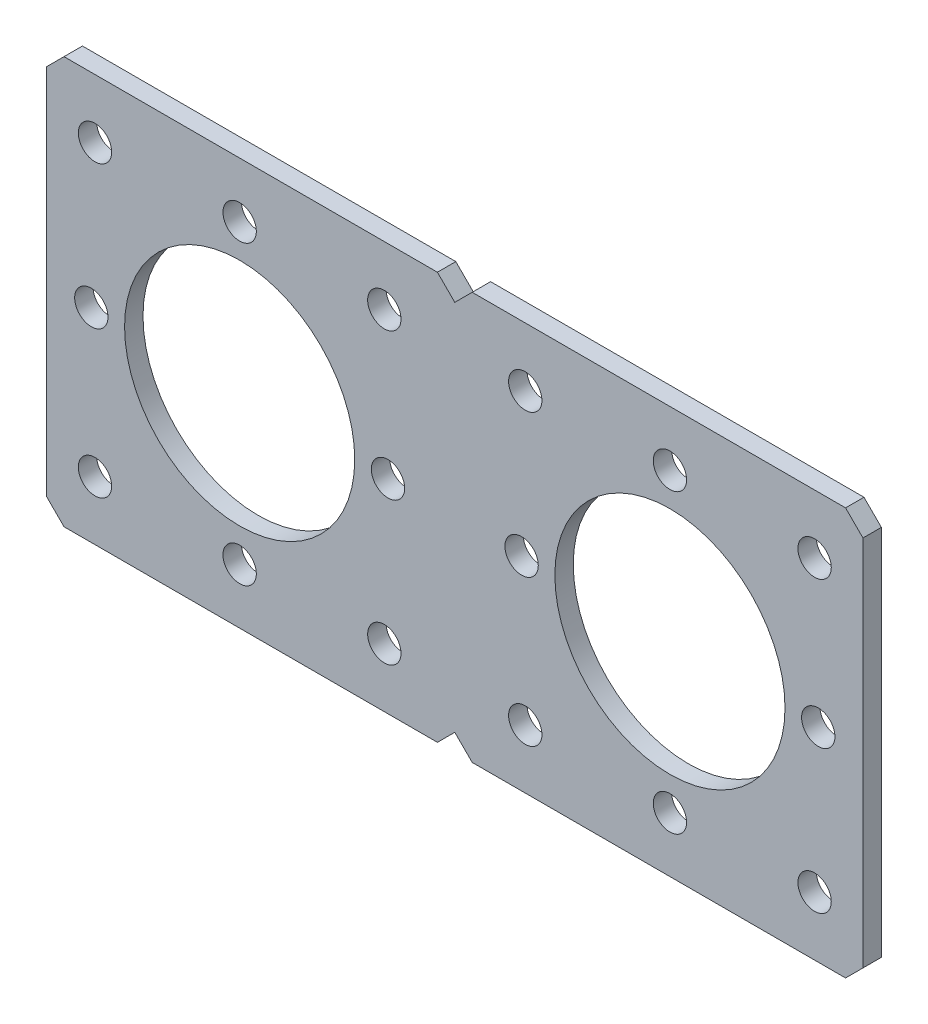
SolidWorks part; units mm, degrees
ref_plane "Front Plane" through (0, 0, 0) normal (0, 0, 1) x (1, 0, 0)
ref_plane "Top Plane" through (0, 0, 0) normal (0, 1, 0) x (1, 0, 0)
ref_plane "Right Plane" through (0, 0, 0) normal (1, 0, 0) x (0, 0, -1)
ref_plane "Plane1" through (0, 0, 0) normal (0, 0, -1) x (-1, 0, 0)
sketch "Sketch1" plane through (0, 0, 0) normal (0, 0, -1) x (-1, 0, 0)
  line L0 (0, -23.114) -> (2.159, -25.273)
  line L1 (2.159, -25.273) -> (48.514, -25.273)
  line L2 (48.514, -25.273) -> (50.673, -23.114)
  line L3 (50.673, -23.114) -> (50.673, 23.114)
  line L4 (50.673, 23.114) -> (48.514, 25.273)
  line L5 (48.514, 25.273) -> (2.159, 25.273)
  line L6 (2.159, 25.273) -> (0, 23.114)
  line L7 (0, 23.114) -> (-2.159, 25.273)
  line L8 (-2.159, 25.273) -> (-48.514, 25.273)
  line L9 (-48.514, 25.273) -> (-50.673, 23.114)
  line L10 (-50.673, 23.114) -> (-50.673, -23.114)
  line L11 (-50.673, -23.114) -> (-48.514, -25.273)
  line L12 (-48.514, -25.273) -> (-2.159, -25.273)
  line L13 (-2.159, -25.273) -> (0, -23.114)
  circle A0 centre (26.7081, -18.415) radius 2.0701
  circle A1 centre (-45.1231, 0) radius 2.0701
  circle A2 centre (26.7081, 18.415) radius 2.0701
  circle A3 centre (-26.7081, 18.415) radius 2.0701
  circle A4 centre (8.7476, 17.9605) radius 2.0701
  circle A5 centre (44.6686, 17.9605) radius 2.0701
  circle A6 centre (26.7081, 0) radius 14.2875
  circle A7 centre (-44.6686, -17.9605) radius 2.0701
  circle A8 centre (-8.7476, 17.9605) radius 2.0701
  circle A9 centre (-26.7081, 0) radius 14.2875
  circle A10 centre (-8.7476, -17.9605) radius 2.0701
  circle A11 centre (-44.6686, 17.9605) radius 2.0701
  circle A12 centre (44.6686, -17.9605) radius 2.0701
  circle A13 centre (8.7476, -17.9605) radius 2.0701
  circle A14 centre (-8.2931, 0) radius 2.0701
  circle A15 centre (45.1231, 0) radius 2.0701
  circle A16 centre (8.2931, 0) radius 2.0701
  circle A17 centre (-26.7081, -18.415) radius 2.0701
extrude "Boss-Extrude1" add sketch "Sketch1" against normal blind 2.286
